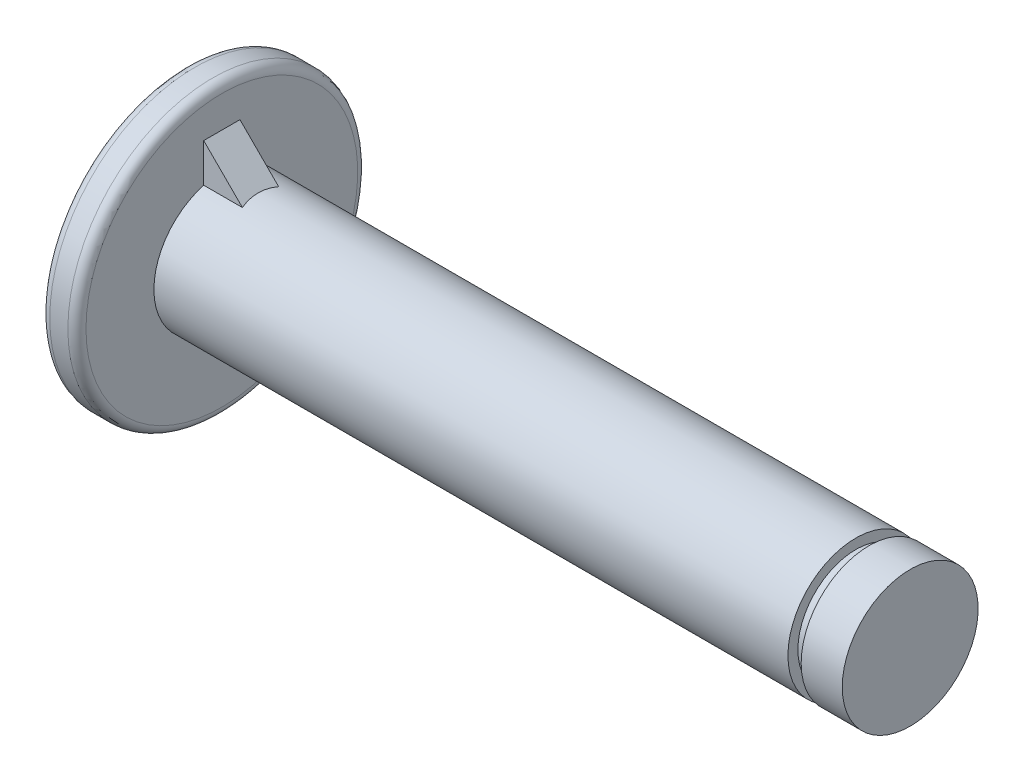
SolidWorks part; units mm, degrees
ref_plane "Front Plane" through (0, 0, 0) normal (0, 0, 1) x (1, 0, 0)
ref_plane "Top Plane" through (0, 0, 0) normal (0, 1, 0) x (1, 0, 0)
ref_plane "Right Plane" through (0, 0, 0) normal (1, 0, 0) x (0, 0, -1)
sketch "Sketch1" plane through (0, 0, 0) normal (0, 0, 1) x (1, 0, 0)
  line L0 (0, 8) -> (0, 0)
  line L1 (0, 0) -> (40, 0)
  line L2 (40, 0) -> (40, 3.75)
  line L3 (40, 3.75) -> (37.73, 3.75)
  line L4 (2, 3.75) -> (2, 8)
  line L5 (2, 8) -> (0, 8)
  line L6 (37, 3.75) -> (37, 3.2)
  line L7 (37, 3.2) -> (37.73, 3.2)
  line L8 (37.73, 3.2) -> (37.73, 3.75)
  line L9 (37, 3.75) -> (2, 3.75)
  dimension "D1" = 40
  dimension "D2" = 8
  dimension "D3" = 3.75
  dimension "D4" = 3
  dimension "D5" = 0.73
  dimension "D6" = 3.2
  dimension "D7" = 2
revolve "Revolve1" add sketch "Sketch1" angle 360 about L1
fillet "Fillet1" radius 0.5 2 edges at (2, 0, 8) (0, 0, 8)
sketch "Sketch2" plane through (0, 0, 0) normal (0, 0, 1) x (1, 0, 0)
  line L0 (4, 3.75) -> (2, 5.75)
  line L1 (37, 3.75) -> (2, 3.75) construction
  dimension "D1" = 2
  dimension "D2" = 45
rib "Rib1" sketch "Sketch2" sketch "Sketch2" thickness 2 extrusion direction parallel to sketch draft on no parameters "D1"=2
